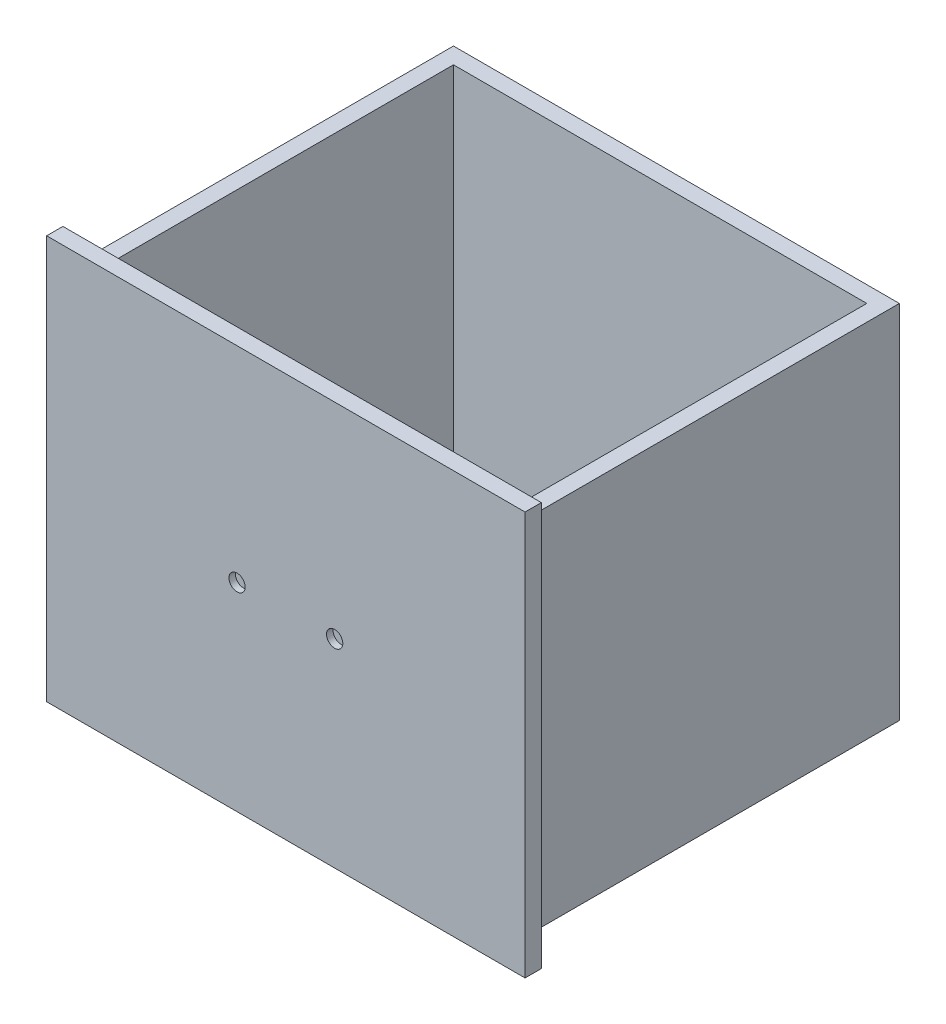
SolidWorks part; units mm, degrees
material "Oak"
ref_plane "Front Plane" through (0, 0, 0) normal (0, 0, 1) x (1, 0, 0)
ref_plane "Top Plane" through (0, 0, 0) normal (0, 1, 0) x (1, 0, 0)
ref_plane "Right Plane" through (0, 0, 0) normal (1, 0, 0) x (0, 0, -1)
sketch "Sketch1" plane through (0, 0, 0) normal (0, 0, 1) x (1, 0, 0)
  line L1 (-186.69, 154.94) -> (186.69, 154.94)
  line L2 (-186.69, 154.94) -> (-186.69, -154.94)
  line L3 (-186.69, -154.94) -> (186.69, -154.94)
  line L4 (186.69, 154.94) -> (186.69, -154.94)
  line L5 (-186.69, 154.94) -> (186.69, -154.94) construction
  line L6 (-186.69, -154.94) -> (186.69, 154.94) construction
  point P0 (0, 0)
  dimension "D1" = 373.38
  dimension "D2" = 309.88
extrude "Boss-Extrude1" add sketch "Sketch1" against normal blind 12.7
ref_plane "Plane1" through (0, 0, -12.7) normal (0, 0, -1) x (-1, 0, 0)
sketch "Sketch2" plane through (0, 0, -12.7) normal (0, 0, -1) x (-1, 0, 0)
  line L0 (-186.69, -154.94) -> (-186.69, 154.94) construction
  line L2 (186.69, 154.94) -> (186.69, -154.94) construction
  line L3 (-186.69, 154.94) -> (186.69, 154.94) construction
  line L10 (-173.99, 142.24) -> (173.99, 142.24)
  line L11 (-173.99, 142.24) -> (-173.99, -139.7)
  line L12 (-173.99, -139.7) -> (173.99, -139.7)
  line L13 (173.99, 142.24) -> (173.99, -139.7)
  dimension "D1" = 12.7
  dimension "D2" = 12.7
  dimension "D3" = 281.94
  dimension "D4" = 12.7
extrude "Boss-Extrude2" add sketch "Sketch2" along normal blind 292.1
ref_plane "Plane2" through (0, 142.24, 0) normal (0, 1, 0) x (1, 0, 0)
sketch "Sketch3" plane through (0, 142.24, 0) normal (0, 1, 0) x (1, 0, 0)
  line L0 (-173.99, 304.8) -> (-173.99, 12.7) construction
  line L1 (173.99, 304.8) -> (173.99, 12.7) construction
  line L5 (-173.99, 12.7) -> (173.99, 12.7) construction
  line L7 (-161.29, 292.1) -> (161.29, 292.1)
  line L8 (-161.29, 292.1) -> (-161.29, 12.7)
  line L9 (-161.29, 12.7) -> (161.29, 12.7)
  line L10 (161.29, 292.1) -> (161.29, 12.7)
  dimension "D1" = 12.7
  dimension "D2" = 279.4
  dimension "D3" = 12.7
extrude "Cut-Extrude1" cut sketch "Sketch3" against normal blind 266.7
ref_plane "Plane3" through (0, 0, 0) normal (0, 0, 1) x (1, 0, 0)
sketch "Sketch4" plane through (0, 0, 0) normal (0, 0, 1) x (1, 0, 0)
  line L1 (-186.69, 154.94) -> (-186.69, -154.94) construction
  line L2 (-186.69, -154.94) -> (186.69, -154.94) construction
  line L3 (186.69, -154.94) -> (186.69, 154.94) construction
  circle A0 centre (-38.1, 0) radius 6.35
  circle A1 centre (38.1, 0) radius 6.35
  point P4 (0, 0)
  dimension "D1" = 76.2
  dimension "D2" = 12.7
  dimension "D3" = 12.7
  dimension "D4" = 148.59
  dimension "D5" = 154.94
  dimension "D6" = 148.59
extrude "Cut-Extrude2" cut sketch "Sketch4" against normal blind 5.08
ref_plane "Plane4" through (0, 0, 0) normal (0, 0, 1) x (1, 0, 0)
sketch "Sketch5" plane through (0, 0, 0) normal (0, 0, 1) x (1, 0, 0)
  line L0 (-186.69, 154.94) -> (-186.69, 160.02)
  line L1 (-186.69, 160.02) -> (186.69, 160.02)
  line L2 (186.69, 160.02) -> (186.69, 154.94)
  line L3 (186.69, 154.94) -> (-186.69, 154.94)
  dimension "D1" = 5.08
extrude "Boss-Extrude3" add sketch "Sketch5" against normal blind 12.7
